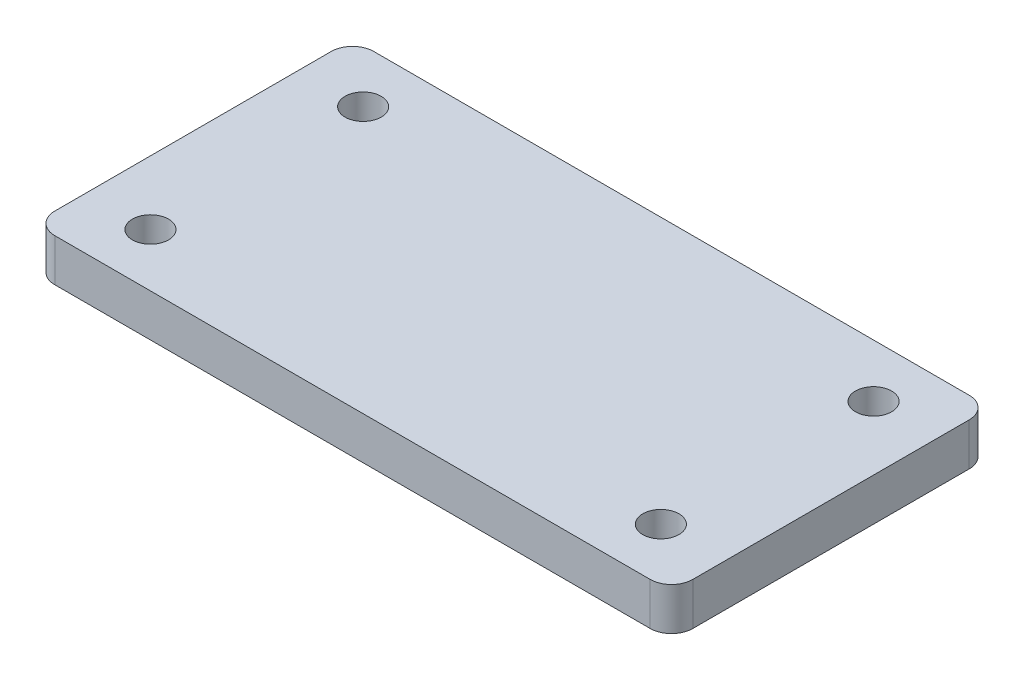
SolidWorks part; units mm, degrees
ref_plane "Alzado" through (0, 0, 0) normal (0, 0, 1) x (1, 0, 0)
ref_plane "Planta" through (0, 0, 0) normal (0, 1, 0) x (1, 0, 0)
ref_plane "Vista lateral" through (0, 0, 0) normal (1, 0, 0) x (0, 0, -1)
sketch "Croquis1" plane through (0, 0, 0) normal (0, 1, 0) x (1, 0, 0)
  line L1 (140, 75) -> (-140, 75)
  line L2 (150, 65) -> (150, -65)
  line L3 (140, -75) -> (-140, -75)
  line L4 (-150, 65) -> (-150, -65)
  line L5 (150, 75) -> (-150, -75) construction
  line L6 (150, -75) -> (-150, 75) construction
  arc A0 (-140, -75) -> (-150, -65) centre (-140, -65) cw
  arc A1 (150, -65) -> (140, -75) centre (140, -65) cw
  arc A2 (140, 75) -> (150, 65) centre (140, 65) cw
  arc A3 (-140, 75) -> (-150, 65) centre (-140, 65) ccw
  point P0 (0, 0)
  dimension "D3" = 10
  dimension "D1" = 300
  dimension "D2" = 150
extrude "Saliente-Extruir2" add sketch "Croquis1" along normal blind 20
sketch "Croquis3" plane through (0, 20, 0) normal (0, 1, 0) x (1, 0, 0)
  line L1 (120, 50) -> (-120, 50)
  line L2 (120, 50) -> (120, -50)
  line L3 (120, -50) -> (-120, -50)
  line L4 (-120, 50) -> (-120, -50)
  line L5 (120, 50) -> (-120, -50) construction
  line L6 (120, -50) -> (-120, 50) construction
  point P0 (0, 0)
hole_wizard "Diámetro de taladro Ø17.0 (17)1" positions "Croquis3D1" profile "Croquis4" hole size "Ø17.0" standard "ISO" end condition up to next
sketch3d "Croquis3D1"
  point P0 (-120, 20, -50)
  point P3 (-120, 20, 50)
  point P6 (120, 20, 50)
  point P9 (120, 20, -50)
sketch "Croquis4" plane through (-120, 20, -50) normal (1, 0, 0) x (0, 0, 1)
  line L0 (0, 0) -> (0, 20)
  line L1 (0, 20) -> (8.5, 20)
  line L2 (8.5, 20) -> (8.5, 0)
  line L5 (8.5, 0) -> (0, 0)
  line L11 (0, -6.35) -> (0, 107.95) construction
  dimension "Diámetro de taladro hasta el siguiente" = 17
  dimension "Profundidad de taladro hasta el siguiente" = 20
hole_wizard "Taladro roscado M161" [suppressed] positions "Croquis3D2" profile "Croquis5" tap size "M16" standard "ISO"
sketch3d "Croquis3D2"
  point P0 (-120, 20, -50)
  point P3 (-120, 20, 50)
  point P6 (120, 20, 50)
  point P9 (120, 20, -50)
sketch "Croquis5" plane through (-120, 20, -50) normal (1, 0, 0) x (0, 0, 1)
  line L0 (0, 0) -> (0, 20)
  line L1 (0, 20) -> (7, 20)
  line L2 (7, 20) -> (7, 0)
  line L5 (7, 0) -> (0, 0)
  line L11 (0, -6.35) -> (0, 107.95) construction
  dimension "Diámetro de perforador para roscar hasta el siguiente" = 14
  dimension "Profundidad de perforador para roscar hasta el siguiente" = 20
cosmetic thread "Rosca de taladro1" [suppressed] parameters "D2"=16
cosmetic thread "Rosca de taladro2" [suppressed] parameters "D2"=16
cosmetic thread "Rosca de taladro3" [suppressed] parameters "D2"=16
cosmetic thread "Rosca de taladro4" [suppressed] parameters "D2"=16
